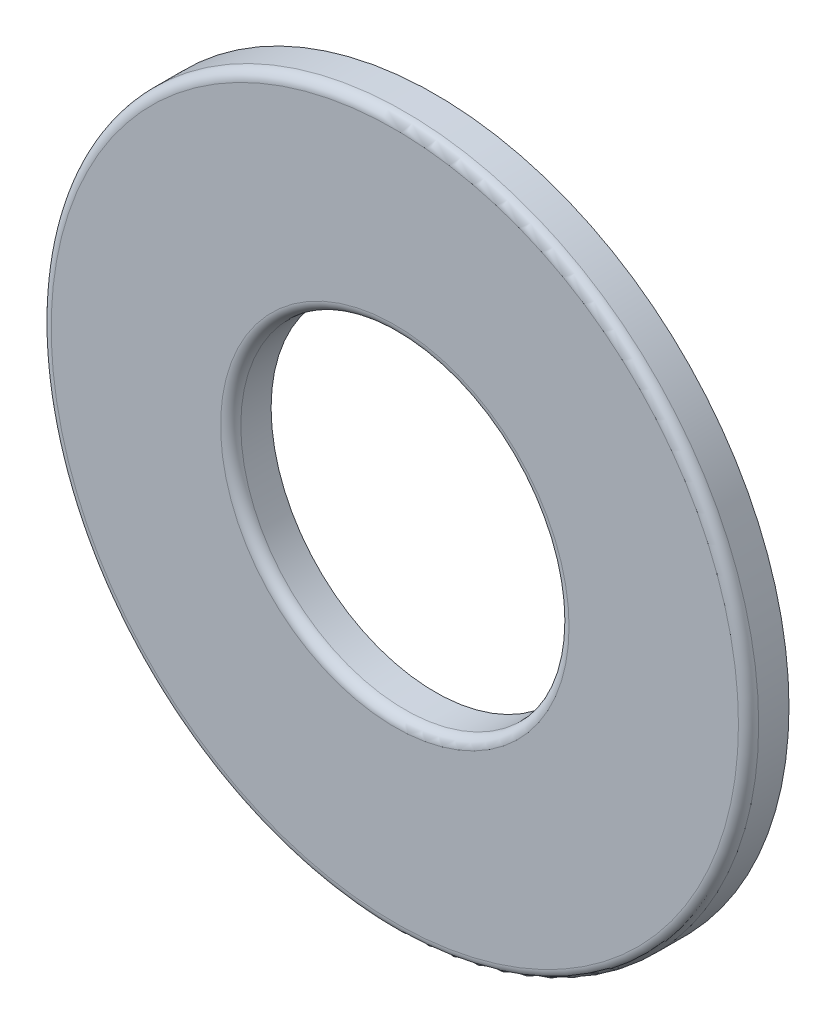
SolidWorks part; units mm, degrees
other "Imported1" parameters "D1"=0.3175, "TH"=1.0287, "Thickness"=1.27
ref_plane "Front Plane" through (0, 0, 0) normal (0, 0, 1) x (1, 0, 0)
ref_plane "Top Plane" through (0, 0, 0) normal (0, 1, 0) x (1, 0, 0)
ref_plane "Right Plane" through (0, 0, 0) normal (1, 0, 0) x (0, 0, -1)
sketch "Sketch1" plane through (0, 0, 0) normal (0, 0, 1) x (1, 0, 0)
  line L0 (-11.1125, 0) -> (11.1125, 0) construction
  line L1 (-5.1562, 0) -> (5.1562, 0) construction
  circle A0 centre (0, 0) radius 5.1562 construction
  circle A1 centre (0, 0) radius 11.1125 construction
  point P8 (0, 0)
  point P9 (0, 11.1125)
  point P11 (5.1562, 0)
  dimension "ID" = 10.3124
  dimension "OD" = 22.225
sketch "Sketch2" plane through (0, 0, 0) normal (1, 0, 0) x (0, 0, -1)
  line L0 (-0.635, 11.1125) -> (0.635, 11.1125) construction
  point P2 (0, 11.1125)
sketch "Sketch3" plane through (0, 0, 0) normal (0, 0, 1) x (1, 0, 0)
  circle A0 centre (0, 0) radius 5.1562
  circle A1 centre (0, 0) radius 11.1125
extrude "Boss-Extrude1" add sketch "Sketch3" along normal up to vertex (0.635 mm away) and the other way up to vertex (0.635 mm away) up to point (0, 11.1125, 0.635) other way up to point (0, 11.1125, -0.635)
fillet "Fillet1" radius 0.3175 2 edges at (11.1125, 0, 0.635) (5.1562, 0, 0.635)
equation "\"D1@Fillet1\"=\"Thickness@Sketch2\"/4"
